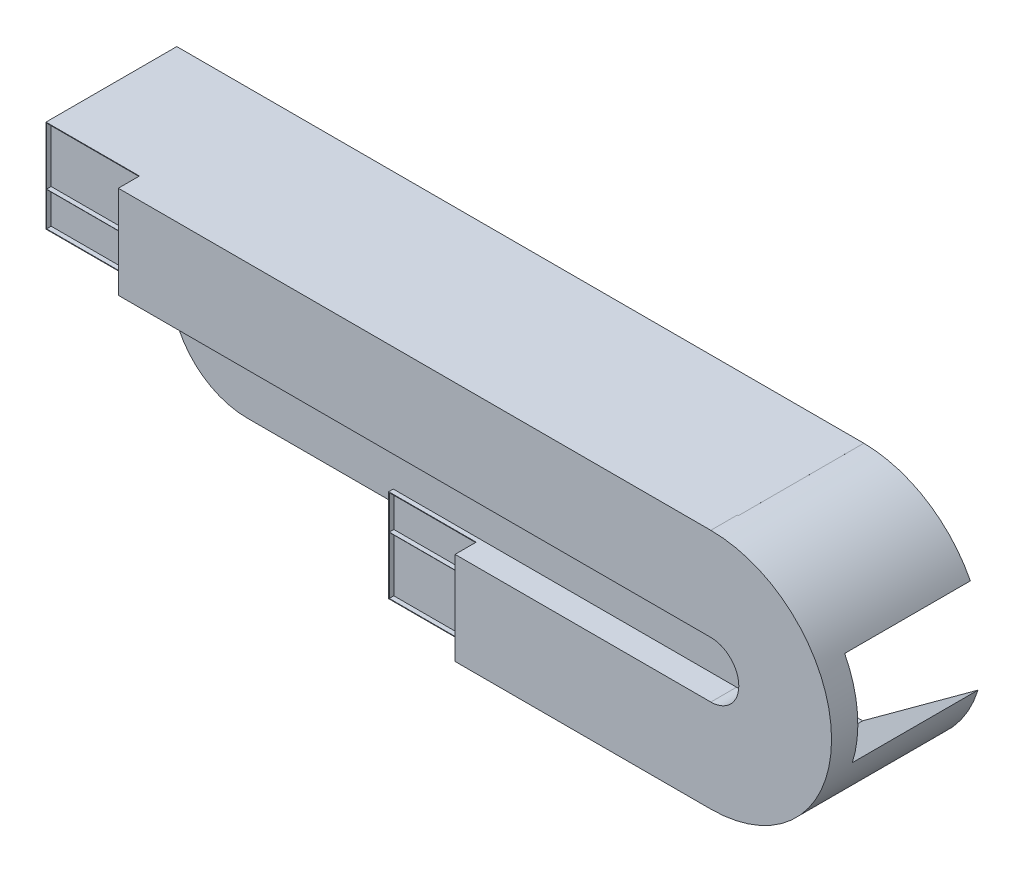
SolidWorks part; units mm, degrees
ref_plane "Piano frontale" through (0, 0, 0) normal (0, 0, 1) x (1, 0, 0)
ref_plane "Piano superiore" through (0, 0, 0) normal (0, 1, 0) x (1, 0, 0)
ref_plane "Piano destro" through (0, 0, 0) normal (1, 0, 0) x (0, 0, -1)
sketch "Schizzo1" plane through (0, 0, 0) normal (0, 0, 1) x (1, 0, 0)
  line L0 (-7028, 842) -> (-7028, 1344)
  line L1 (-1028, 842) -> (-7028, 842) construction
  line L2 (-7028, 842) -> (-7028, 542)
  line L4 (-7028, 1344) -> (-1028, 1344)
  line L5 (-7028, 542) -> (-1028, 542)
  line L6 (-1028, 42) -> (-4028, 42)
  line L7 (-1028, -760) -> (-4028, -760)
  line L8 (-4028, -760) -> (-4028, 42)
  arc A0 (-1028, 42) -> (-1028, 542) centre (-1028, 292) ccw
  arc A1 (-1028, -760) -> (-1028, 1344) centre (-1028, 292) ccw
  dimension "D4" = 500
  dimension "D1" = 502
  dimension "D2" = 300
extrude "Estrusione-Estrusione1" add sketch "Schizzo1" along normal blind 5 from offset 1100
sketch "Schizzo2" plane through (0, 0, 1105) normal (0, 0, 1) x (1, 0, 0)
  line L0 (-1028, 1349) -> (-7033, 1349)
  line L1 (-7033, 1349) -> (-7033, 537)
  line L2 (-7033, 537) -> (-1028, 537)
  line L3 (-1028, 47) -> (-4033, 47)
  line L4 (-4033, 47) -> (-4033, -765)
  line L5 (-4033, -765) -> (-1028, -765)
  line L6 (-1028, 1344) -> (-7028, 1344)
  line L7 (-7028, 1344) -> (-7028, 542)
  line L8 (-7028, 542) -> (-1028, 542)
  line L9 (-1028, 42) -> (-4028, 42)
  line L10 (-4028, 42) -> (-4028, -760)
  line L11 (-4028, -760) -> (-1028, -760)
  line L12 (-1028, 1344) -> (-7028, 1344)
  line L13 (-7028, 1344) -> (-7028, 542)
  line L14 (-7028, 542) -> (-1028, 542)
  line L15 (-1028, 42) -> (-4028, 42)
  line L16 (-4028, 42) -> (-4028, -760)
  line L17 (-4028, -760) -> (-1028, -760)
  arc A0 (-1028, 47) -> (-1028, 537) centre (-1028, 292) ccw
  arc A1 (-1028, -765) -> (-1028, 1349) centre (-1028, 292) ccw
  arc A2 (-1028, 42) -> (-1028, 542) centre (-1028, 292) ccw
  arc A3 (-1028, -760) -> (-1028, 1344) centre (-1028, 292) ccw
  arc A4 (-1028, 42) -> (-1028, 542) centre (-1028, 292) ccw
  arc A5 (-1028, -760) -> (-1028, 1344) centre (-1028, 292) ccw
  dimension "D1" = 0
  dimension "D2" = 5
extrude "Estrusione-Estrusione2" add sketch "Schizzo2" along normal blind 40 and the other way blind 5
sketch "Schizzo3" plane through (0, 0, 1105) normal (0, 0, 1) x (1, 0, 0)
  line L4 (-4028, -259) -> (-1028, -259)
  line L5 (-1028, 843) -> (-7028, 843)
  line L8 (-7028, 841) -> (-7028, 843)
  line L9 (-7028, 542) -> (-1028, 542) construction
  line L10 (-7028, 841) -> (-1028, 841)
  line L11 (-1028, -257) -> (-4028, -257)
  line L12 (-4028, -259) -> (-4028, -257)
  line L13 (-1028, 42) -> (-4028, 42) construction
  arc A0 (-1028, -257) -> (-1028, 841) centre (-1028, 292) ccw
  arc A5 (-1028, 42) -> (-1028, 542) centre (-1028, 292) ccw construction
  arc A6 (-1028, -259) -> (-1028, 843) centre (-1028, 292) ccw
  dimension "D5" = 0
  dimension "D2" = 2
  dimension "D1" = 299
  dimension "D3" = 299
  dimension "D4" = 2
extrude "Estrusione-Estrusione3" add sketch "Schizzo3" along normal up to surface (40 mm away) up to face at (-3117.75, 292, 1145)
sketch "Schizzo4" plane through (0, 0, 1145) normal (0, 0, 1) x (1, 0, 0)
  line L0 (-1028, 1344) -> (-7028, 1344) construction
  line L1 (-7028, 542) -> (-1028, 542) construction
  line L2 (-1028, 42) -> (-4028, 42) construction
  line L4 (-1028, 1344) -> (-6214.9945, 1344)
  line L5 (-6214.9945, 542) -> (-1028, 542)
  line L6 (-1028, 1349) -> (-7033, 1349)
  line L7 (-7033, 1349) -> (-7033, 537)
  line L8 (-7033, 537) -> (-1028, 537)
  line L9 (-1028, 47) -> (-4033, 47)
  line L10 (-4033, 47) -> (-4033, -765)
  line L11 (-4033, -765) -> (-1028, -765)
  line L12 (-1028, 1349) -> (-6214.9945, 1349)
  line L14 (-6214.9945, 537) -> (-1028, 537)
  line L15 (-1028, 47) -> (-3267.0968, 47)
  line L17 (-3267.0968, -765) -> (-1028, -765)
  line L18 (-1028, 42) -> (-3267.0968, 42)
  line L19 (-6214.9945, 542) -> (-6214.9945, 537)
  line L20 (-3267.0968, -765) -> (-3267.0968, -760)
  line L21 (-6214.9945, 1349) -> (-6214.9945, 1344)
  line L22 (-1028, -760) -> (-3267.0968, -760)
  line L23 (-4028, -760) -> (-1028, -760) construction
  line L24 (-3267.0968, 42) -> (-3267.0968, 47)
  arc A0 (-1028, 42) -> (-1028, 542) centre (-1028, 292) ccw construction
  arc A1 (-1028, 42) -> (-1028, 542) centre (-1028, 292) ccw
  arc A2 (-1028, -765) -> (-1028, 1349) centre (-1028, 292) ccw
  arc A3 (-1028, 47) -> (-1028, 537) centre (-1028, 292) ccw
  arc A4 (-1028, -765) -> (-1028, 1349) centre (-1028, 292) ccw
  arc A5 (-1028, 47) -> (-1028, 537) centre (-1028, 292) ccw
  arc A6 (-1028, -760) -> (-1028, 1344) centre (-1028, 292) ccw construction
  arc A7 (-1028, -760) -> (-1028, 1344) centre (-1028, 292) ccw
  dimension "D1" = 0
extrude "Estrusione-Estrusione4" add sketch "Schizzo4" along normal blind 180
sketch "Schizzo7" plane through (0, 0, 1325) normal (0, 0, 1) x (1, 0, 0)
  line L0 (-3267.0968, 42) -> (-3267.0968, -760)
  line L1 (-6214.9945, 1344) -> (-6214.9945, 542)
  line L6 (-1028, -760) -> (-3267.0968, -760)
  line L7 (-3267.0968, -760) -> (-3267.0968, -765)
  line L8 (-3267.0968, -765) -> (-1028, -765)
  line L9 (-1028, 1349) -> (-6214.9945, 1349)
  line L10 (-6214.9945, 1349) -> (-6214.9945, 1344)
  line L11 (-6214.9945, 1344) -> (-1028, 1344)
  line L13 (-3267.0968, -760) -> (-3267.0968, -765)
  line L14 (-3267.0968, -765) -> (-1028, -765)
  line L15 (-1028, 1349) -> (-6214.9945, 1349)
  line L16 (-6214.9945, 1349) -> (-6214.9945, 1344)
  line L18 (-1028, 47) -> (-3267.0968, 47)
  line L19 (-3267.0968, 47) -> (-3267.0968, 42)
  line L20 (-3267.0968, 42) -> (-1028, 42)
  line L21 (-1028, 542) -> (-6214.9945, 542)
  line L22 (-6214.9945, 542) -> (-6214.9945, 537)
  line L23 (-6214.9945, 537) -> (-1028, 537)
  line L24 (-1028, 47) -> (-3267.0968, 47)
  line L25 (-3267.0968, 47) -> (-3267.0968, 42)
  line L28 (-6214.9945, 542) -> (-6214.9945, 537)
  line L29 (-6214.9945, 537) -> (-1028, 537)
  arc A2 (-1028, -760) -> (-1028, 1344) centre (-1028, 292) ccw
  arc A3 (-1028, -765) -> (-1028, 1349) centre (-1028, 292) ccw
  arc A5 (-1028, -765) -> (-1028, 1349) centre (-1028, 292) ccw
  arc A6 (-1028, 47) -> (-1028, 537) centre (-1028, 292) ccw
  arc A7 (-1028, 42) -> (-1028, 542) centre (-1028, 292) ccw
  arc A8 (-1028, 47) -> (-1028, 537) centre (-1028, 292) ccw
  dimension "D1" = 0
  dimension "D2" = 0
extrude "Estrusione-Estrusione5" add sketch "Schizzo7" along normal blind 5
sketch "Schizzo14" plane through (0, 0, 1100) normal (0, 0, -1) x (-1, 0, 0)
  line L0 (7033, 1344) -> (7033, 1349)
  line L1 (7028, 814.8405) -> (7033, 814.8405)
  line L2 (7028, 814.8405) -> (7028, 1344)
  line L4 (7033, 814.8405) -> (7033, 1344)
  line L5 (7028, 1349) -> (1018.379, 1349)
  line L7 (7028, 1344) -> (1018.379, 1344)
  line L8 (1018.379, 1349) -> (1018.379, 1344)
  line L9 (7033, 1349) -> (7028, 1349)
  dimension "D1" = 5
  dimension "D2" = 5
extrude "Estrusione-Estrusione10" add sketch "Schizzo14" along normal up to vertex (1100 mm away)
sketch "Schizzo15" plane through (0, 0, 1100) normal (0, 0, -1) x (-1, 0, 0)
  line L0 (1018.379, 1348.9562) -> (1018.379, 1344)
  line L1 (1018.379, 1344) -> (86.001, 771.4651)
  arc A0 (1018.379, 1348.9562) -> (1028, -765) centre (1028, 292) ccw construction
  arc A1 (1018.379, 1348.9562) -> (86.001, 771.4651) centre (1028, 292) ccw
extrude "Estrusione-Estrusione11" add sketch "Schizzo15" along normal up to surface (1100 mm away) up to face at (-5026.4597, 1169.2802, 0)
sketch "Schizzo16" plane through (0, 0, 1100) normal (0, 0, -1) x (-1, 0, 0)
  line L0 (1028, -760) -> (19.0384, -23.0324)
  line L1 (4001.2709, -765) -> (1028, -765)
  line L3 (4001.2709, -760) -> (1028, -760)
  line L5 (4033, -760) -> (4033, -765)
  line L7 (4033, -760) -> (4033, -10.8926)
  line L8 (4033, -10.8926) -> (4001.2709, -10.8926)
  line L9 (4001.2709, -760) -> (4001.2709, -10.8926)
  line L10 (4033, -765) -> (4001.2709, -765)
  arc A0 (86.001, 771.4651) -> (1028, -765) centre (1028, 292) ccw construction
  arc A1 (19.0384, -23.0324) -> (1028, -765) centre (1028, 292) ccw
extrude "Estrusione-Estrusione12" add sketch "Schizzo16" along normal up to surface (1100 mm away) up to face at (-3897.7974, 1158.3113, 0)
sketch "Schizzo17" plane through (-4033, 0, 0) normal (-1, 0, 0) x (0, 0, 1)
  line L0 (0, -765) -> (0, -10.8926) construction
  line L1 (1100, -10.8926) -> (0, -10.8926)
  line L2 (1100, -10.8926) -> (1100, -54.769)
  line L3 (1100, -54.769) -> (0, -54.769)
  line L4 (0, -10.8926) -> (0, -54.769)
extrude "Estrusione-Estrusione13" add sketch "Schizzo17" along normal blind 2559
sketch "Schizzo18" plane through (0, 0, 1100) normal (0, 0, 1) x (1, 0, 0)
  line L0 (-7033, 537) -> (-6214.9945, 537) construction
  line L1 (-6592, -54.769) -> (-4033, -54.769) construction
  line L2 (-6147.5595, 537) -> (-4030.5, 537)
  line L3 (-4030.5, 537) -> (-4033, -54.769)
  line L4 (-4033, -54.769) -> (-5312.5, -54.769)
  arc A0 (-5937.6725, 388.2625) -> (-6147.5595, 537) centre (-6147.5595, 314.543) ccw
  arc A1 (-5937.6725, 388.2625) -> (-5312.5, -54.769) centre (-5312.5, 607.8448) ccw
  point P1 (0, 0)
  point P6 (0, 0)
  point P12 (-7033, 537)
  point P17 (-6147.5595, 542)
  point P18 (-6592, -54.769)
  point P19 (-5312.5, -54.769)
extrude "Estrusione-Estrusione14" add sketch "Schizzo18" along normal blind 5
sketch "Schizzo19" plane through (-4032.6966, 17.0366, 0) normal (1, -0.0042, 0) x (0, 0, -1)
  line L4 (-1105, 29.9637) -> (-1100, 29.9637)
  line L5 (-1100, 29.9637) -> (-1100, 519.968)
  line L6 (-1100, 519.968) -> (-1105, 519.968)
  line L7 (-1105, 519.968) -> (-1105, 29.9637)
  line L8 (-1105, 29.9637) -> (-1100, 29.9637)
  line L9 (-1100, 29.9637) -> (-1100, 519.968)
  line L10 (-1100, 519.968) -> (-1105, 519.968)
  line L11 (-1105, 519.968) -> (-1105, 29.9637)
  dimension "D1" = 0
extrude "Estrusione-Estrusione15" add sketch "Schizzo19" along normal blind 3500
sketch "Schizzo20" plane through (0, 0, 1100) normal (0, 0, 1) x (1, 0, 0)
  line L0 (-5312.5, -54.769) -> (-5312.5, -181.3418)
  line L1 (-5312.5, -181.3418) -> (-6649.4826, -181.3418)
  line L2 (-6649.4826, -181.3418) -> (-6649.4826, 67.2177)
  line L3 (-6649.4826, 67.2177) -> (-5695.618, 67.2177)
  arc A0 (-5937.6725, 388.2625) -> (-5312.5, -54.769) centre (-5312.5, 607.8448) ccw construction
  arc A1 (-5695.618, 67.2177) -> (-5312.5, -54.769) centre (-5312.5, 607.8448) ccw
extrude "Taglio-Estrusione1" cut sketch "Schizzo20" against normal blind 3500
